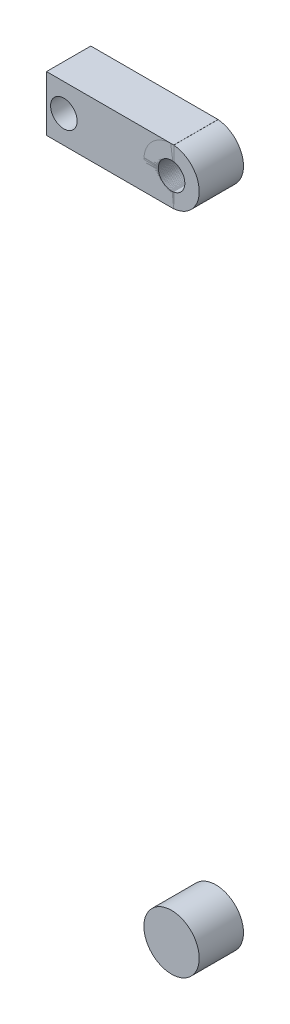
SolidWorks part; units mm, degrees
ref_plane "Plano frontal" through (0, 0, 0) normal (0, 0, 1) x (1, 0, 0)
ref_plane "Plano superior" through (0, 0, 0) normal (0, 1, 0) x (1, 0, 0)
ref_plane "Plano direito" through (0, 0, 0) normal (1, 0, 0) x (0, 0, -1)
sketch "Esboço1" plane through (0, 0, 0) normal (0, 0, 1) x (1, 0, 0)
  circle A0 centre (11.4981, 4.9034) radius 12.5
  circle A1 centre (11.4981, -295.0966) radius 12.5
  dimension "D1" = 25
  dimension "D4" = 25
  dimension "D5" = 300
extrude "Ressalto-extrusão6" add sketch "Esboço1" along normal blind 20
sketch "Esboço3" plane through (0, 0, 0) normal (1, 0, 0) x (0, 0, -1)
  line L0 (-20, 17.4034) -> (-20, -7.5966) construction
  line L1 (0, -7.5966) -> (-20, -7.5966)
  line L2 (0, -7.5966) -> (0, 17.4034)
  line L3 (0, 17.4034) -> (-20, 17.4034)
  line L4 (-20, -7.5966) -> (-20, 17.4034)
extrude "Ressalto-extrusão7" add sketch "Esboço3" against normal blind 45 and the other way blind 12.5 separate body
sketch "Esboço4" plane through (0, 0, 20) normal (0, 0, 1) x (1, 0, 0)
  circle A0 centre (11.4981, 4.9034) radius 6
  circle A1 centre (-37.1656, 4.9034) radius 6
  dimension "D1" = 12
  dimension "D2" = 12
extrude "Corte-extrusão1" cut sketch "Esboço4" against normal blind 45
